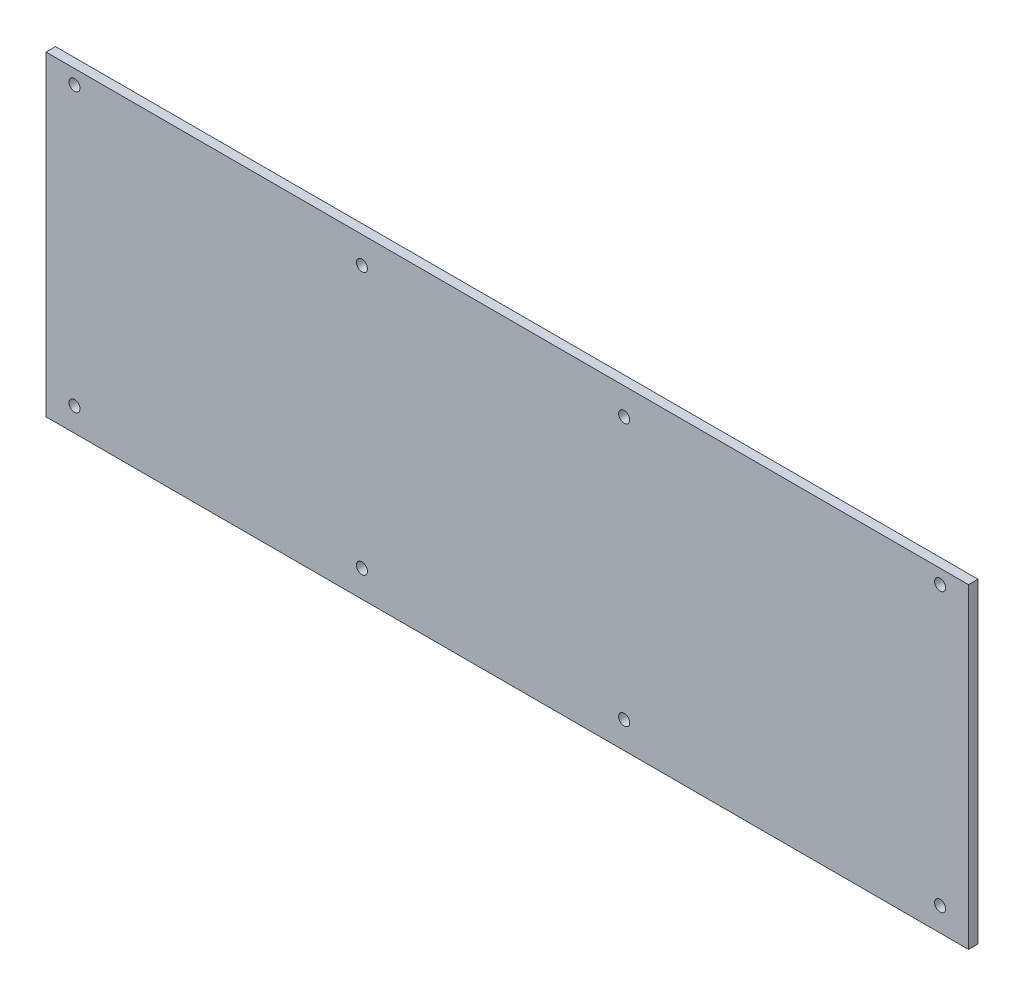
SolidWorks part; units mm, degrees
ref_plane "Front Plane" through (0, 0, 0) normal (0, 0, 1) x (1, 0, 0)
ref_plane "Top Plane" through (0, 0, 0) normal (0, 1, 0) x (1, 0, 0)
ref_plane "Right Plane" through (0, 0, 0) normal (1, 0, 0) x (0, 0, -1)
sketch "Sketch1" plane through (0, 0, 0) normal (0, 0, 1) x (1, 0, 0)
  line L1 (0, 0) -> (300, 0)
  line L2 (0, 0) -> (0, 100)
  line L3 (0, 100) -> (300, 100)
  line L4 (300, 0) -> (300, 100)
  dimension "D1" = 300
  dimension "D2" = 100
extrude "Boss-Extrude1" add sketch "Sketch1" along normal blind 3
sketch "Sketch3" plane through (0, 0, 0) normal (0, 0, -1) x (-1, 0, 0)
  line L0 (0, 0) -> (-300, 0) construction
  line L1 (0, 100) -> (-8, 100)
  line L2 (0, 100) -> (0, 0)
  line L3 (0, 0) -> (-8, 0)
  line L4 (-8, 100) -> (-8, 0)
  dimension "D1" = 8
extrude "Cut-Extrude2" cut sketch "Sketch3" against normal blind 10
sketch "Sketch4" plane through (0, 0, 0) normal (0, 0, -1) x (-1, 0, 0)
  line L0 (-300, 0) -> (-300, 100) construction
  line L1 (-300, 100) -> (-8, 100) construction
  line L2 (-154, 100) -> (-154, 75.8686) construction
  line L3 (-8, 0) -> (-300, 0) construction
  line L4 (-300, 0) -> (-300, 100) construction
  circle A0 centre (-291, 95.5) radius 1.75
  circle A3 centre (-17, 95.5) radius 1.75
  circle A4 centre (-17, 7.5) radius 1.75
  circle A5 centre (-291, 7.5) radius 1.75
  dimension "D4" = 3.5
  dimension "D8" = 9
  dimension "D9" = 3.5
  dimension "D1" = 9
  dimension "D2" = 4.5
  dimension "D5" = 7.5
extrude "Cut-Extrude3" cut sketch "Sketch4" against normal through all
sketch "Sketch7" plane through (0, 0, 0) normal (0, 0, -1) x (-1, 0, 0)
  line L0 (-8, 100) -> (-8, 0) construction
  line L1 (-8, 50) -> (-81.4797, 50) construction
  line L2 (-149.5, 100) -> (-149.5, 67.5873) construction
  line L3 (-300, 100) -> (-8, 100) construction
  circle A0 centre (-108, 91.5) radius 1.75
  circle A1 centre (-191, 91.5) radius 1.75
  circle A2 centre (-191, 8.5) radius 1.75
  circle A3 centre (-108, 8.5) radius 1.75
  dimension "D1" = 3.5
  dimension "D2" = 100
  dimension "D3" = 83
  dimension "D4" = 83
extrude "Cut-Extrude6" cut sketch "Sketch7" against normal through all
